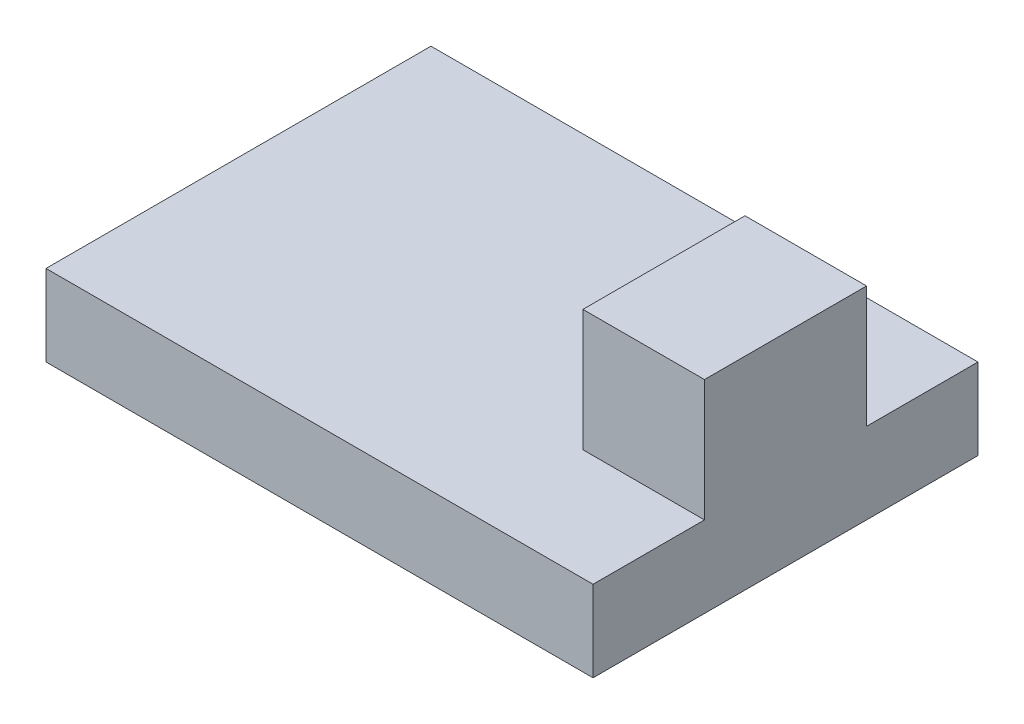
SolidWorks part; units mm, degrees
material "Sculpteo SLS"
ref_plane "Front Plane" through (0, 0, 0) normal (0, 0, 1) x (1, 0, 0)
ref_plane "Top Plane" through (0, 0, 0) normal (0, 1, 0) x (1, 0, 0)
ref_plane "Right Plane" through (0, 0, 0) normal (1, 0, 0) x (0, 0, -1)
sketch "Sketch1" plane through (0, 0, 0) normal (0, 1, 0) x (1, 0, 0)
  line L1 (13.5, -9.5) -> (-13.5, -9.5)
  line L2 (13.5, -9.5) -> (13.5, 9.5)
  line L3 (13.5, 9.5) -> (-13.5, 9.5)
  line L4 (-13.5, -9.5) -> (-13.5, 9.5)
  line L5 (13.5, -9.5) -> (-13.5, 9.5) construction
  line L6 (13.5, 9.5) -> (-13.5, -9.5) construction
  point P0 (0, 0)
  dimension "D1" = 27
  dimension "D2" = 19
extrude "Boss-Extrude1" add sketch "Sketch1" along normal blind 4
sketch "Sketch2" plane through (0, 4, 0) normal (0, 1, 0) x (1, 0, 0)
  line L0 (13.5, -9.5) -> (13.5, 9.5) construction
  line L1 (13.5, 4) -> (7.5, 4)
  line L2 (13.5, 4) -> (13.5, -4)
  line L3 (13.5, -4) -> (7.5, -4)
  line L4 (7.5, 4) -> (7.5, -4)
  point P6 (7.5, 0)
  dimension "D1" = 6
  dimension "D2" = 8
extrude "Boss-Extrude2" add sketch "Sketch2" along normal blind 6
